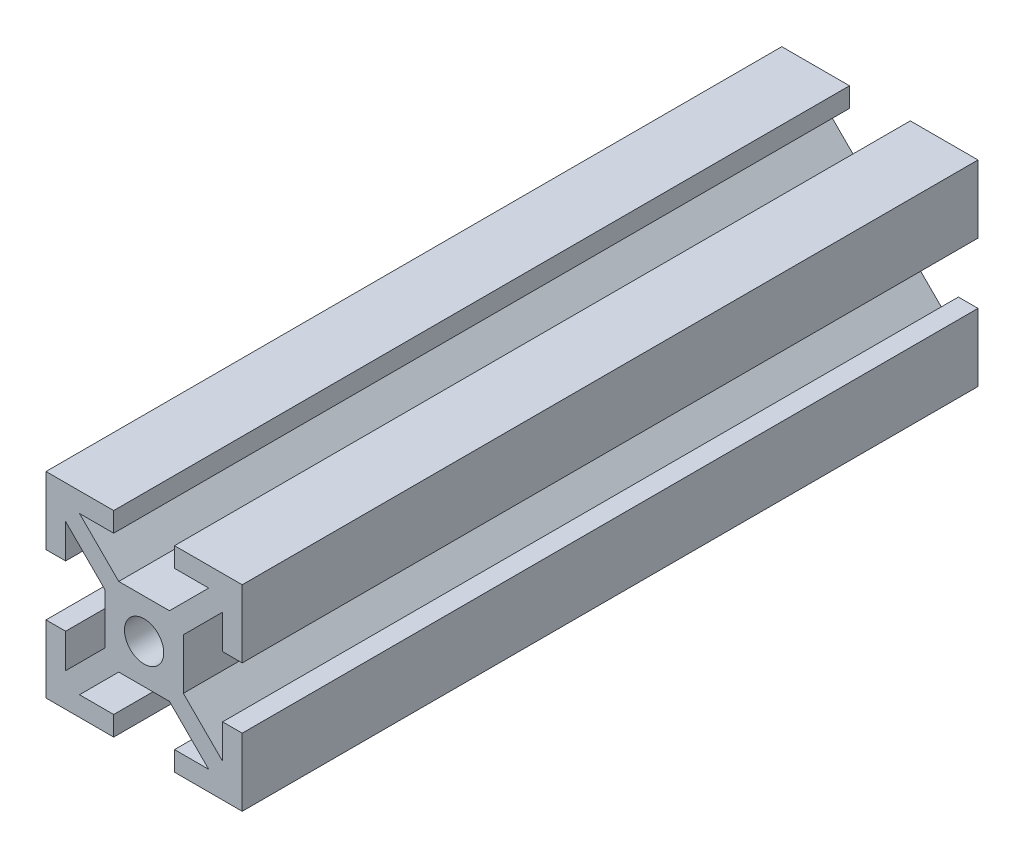
SolidWorks part; units mm, degrees
ref_plane "Front Plane" through (0, 0, 0) normal (0, 0, 1) x (1, 0, 0)
ref_plane "Top Plane" through (0, 0, 0) normal (0, 1, 0) x (1, 0, 0)
ref_plane "Right Plane" through (0, 0, 0) normal (1, 0, 0) x (0, 0, -1)
sketch "Sketch1" plane through (0, 0, 0) normal (0, 0, 1) x (1, 0, 0)
  line L0 (-10, 10) -> (0, 0) construction
  line L2 (0, 0) -> (0, 2.5) construction
  line L3 (-3.1, 10) -> (-10, 10)
  line L6 (0, 0) -> (0, 2.5) construction
  line L7 (2.5858, 4) -> (-2.5858, 4)
  line L11 (-3.1, 8) -> (-6.5858, 8)
  line L13 (-3.1, 10) -> (-3.1, 8)
  line L14 (-8, 6.5858) -> (-4, 2.5858)
  line L15 (-6.5858, 8) -> (-2.5858, 4)
  line L16 (-10, 3.1) -> (-8, 3.1)
  line L17 (-8, 3.1) -> (-8, 6.5858)
  line L19 (-4, -2.5858) -> (-4, 2.5858)
  line L21 (-10, 3.1) -> (-10, 10)
  line L22 (0, 0) -> (0, 13.8386) construction
  line L23 (0, 0) -> (-17.8283, 0) construction
  line L24 (10, 3.1) -> (10, 10)
  line L25 (8, 3.1) -> (8, 6.5858)
  line L26 (10, 3.1) -> (8, 3.1)
  line L27 (6.5858, 8) -> (2.5858, 4)
  line L28 (8, 6.5858) -> (4, 2.5858)
  line L29 (3.1, 10) -> (3.1, 8)
  line L30 (3.1, 8) -> (6.5858, 8)
  line L31 (3.1, 10) -> (10, 10)
  line L32 (-6.5858, -8) -> (-2.5858, -4)
  line L33 (-3.1, -10) -> (-3.1, -8)
  line L34 (10, -3.1) -> (8, -3.1)
  line L35 (10, -3.1) -> (10, -10)
  line L36 (8, -3.1) -> (8, -6.5858)
  line L37 (8, -6.5858) -> (4, -2.5858)
  line L38 (6.5858, -8) -> (2.5858, -4)
  line L39 (3.1, -8) -> (6.5858, -8)
  line L40 (3.1, -10) -> (10, -10)
  line L41 (3.1, -10) -> (3.1, -8)
  line L42 (-3.1, -8) -> (-6.5858, -8)
  line L43 (-8, -6.5858) -> (-4, -2.5858)
  line L44 (-8, -3.1) -> (-8, -6.5858)
  line L45 (-10, -3.1) -> (-8, -3.1)
  line L46 (-10, -3.1) -> (-10, -10)
  line L47 (-3.1, -10) -> (-10, -10)
  line L48 (4, -2.5858) -> (4, 2.5858)
  line L49 (2.5858, -4) -> (-2.5858, -4)
  circle A0 centre (0, 0) radius 2
  point P50 (4, 0)
  dimension "D3" = 8
  dimension "D8" = 4
  dimension "D1" = 4
  dimension "D2" = 10
  dimension "D4" = 2
  dimension "D7" = 3.1
  dimension "D9" = 1
extrude "Boss-Extrude1" add sketch "Sketch1" along normal blind 75
